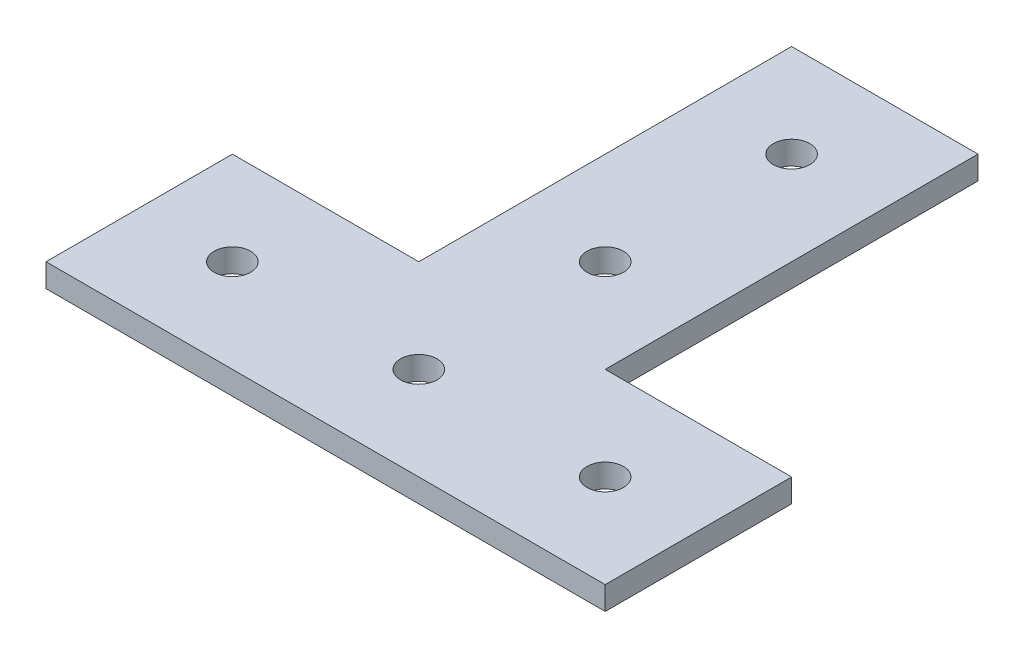
SolidWorks part; units mm, degrees
material "6061-T6 (SS)"
ref_plane "Front Plane" through (0, 0, 0) normal (0, 0, 1) x (1, 0, 0)
ref_plane "Top Plane" through (0, 0, 0) normal (0, 1, 0) x (1, 0, 0)
ref_plane "Right Plane" through (0, 0, 0) normal (1, 0, 0) x (0, 0, -1)
sketch "Sketch1" plane through (0, 0, 0) normal (0, 1, 0) x (1, 0, 0)
  line L0 (38.1, 0) -> (-38.1, 0)
  line L1 (-38.1, 0) -> (-38.1, 25.4)
  line L2 (-38.1, 25.4) -> (-12.7, 25.4)
  line L3 (-12.7, 25.4) -> (-12.7, 76.2)
  line L4 (-12.7, 76.2) -> (12.7, 76.2)
  line L5 (12.7, 76.2) -> (12.7, 25.4)
  line L6 (12.7, 25.4) -> (38.1, 25.4)
  line L7 (38.1, 25.4) -> (38.1, 0)
  line L8 (25.4, 12.7) -> (-25.4, 12.7) construction
  line L9 (0, 12.7) -> (0, 38.1) construction
  line L10 (0, 38.1) -> (0, 63.5) construction
  line L11 (0, 63.5) -> (0, 76.2) construction
  line L12 (38.1, 12.7) -> (-38.1, 12.7) construction
  circle A0 centre (0, 63.5) radius 2.4892
  circle A1 centre (0, 38.1) radius 2.4892
  circle A2 centre (-25.4, 12.7) radius 2.4892
  circle A3 centre (25.4, 12.7) radius 2.4892
  circle A4 centre (0, 12.7) radius 2.4892
  point P4 (0, 0)
  point P24 (0, 12.7)
  point P27 (0, 12.7)
  dimension "D4" = 4.9784
  dimension "D5" = 12.7
  dimension "D6" = 25.4
  dimension "D1" = 25.4
  dimension "D2" = 76.2
  dimension "D3" = 50.8
  dimension "D7" = 50.8
extrude "Boss-Extrude1" add sketch "Sketch1" along normal blind 3.175
equation "\"Thick\"= \"in\""
